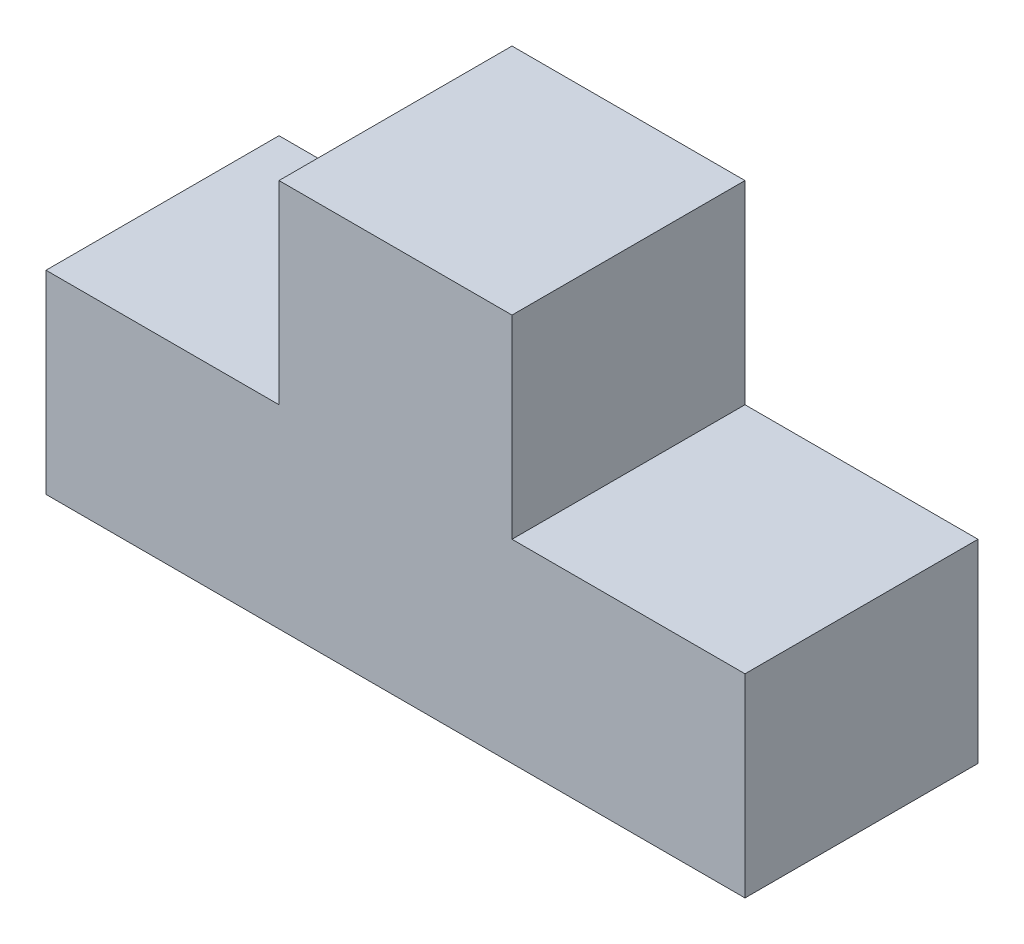
SolidWorks part; units mm, degrees
ref_plane "Front Plane" through (0, 0, 0) normal (0, 0, 1) x (1, 0, 0)
ref_plane "Top Plane" through (0, 0, 0) normal (0, 1, 0) x (1, 0, 0)
ref_plane "Right Plane" through (0, 0, 0) normal (1, 0, 0) x (0, 0, -1)
sketch "Sketch1" plane through (0, 0, 0) normal (0, 0, 1) x (1, 0, 0)
  line L0 (0, 0) -> (90, 0)
  line L1 (90, 0) -> (90, 25)
  line L2 (90, 25) -> (60, 25)
  line L3 (60, 25) -> (60, 50)
  line L4 (60, 50) -> (30, 50)
  line L5 (30, 50) -> (30, 25)
  line L6 (30, 25) -> (0, 25)
  line L7 (0, 25) -> (0, 0)
  dimension "D1" = 90
  dimension "D2" = 25
  dimension "D3" = 25
  dimension "D4" = 30
  dimension "D5" = 25
  dimension "D6" = 30
extrude "Boss-Extrude1" add sketch "Sketch1" along normal blind 30
